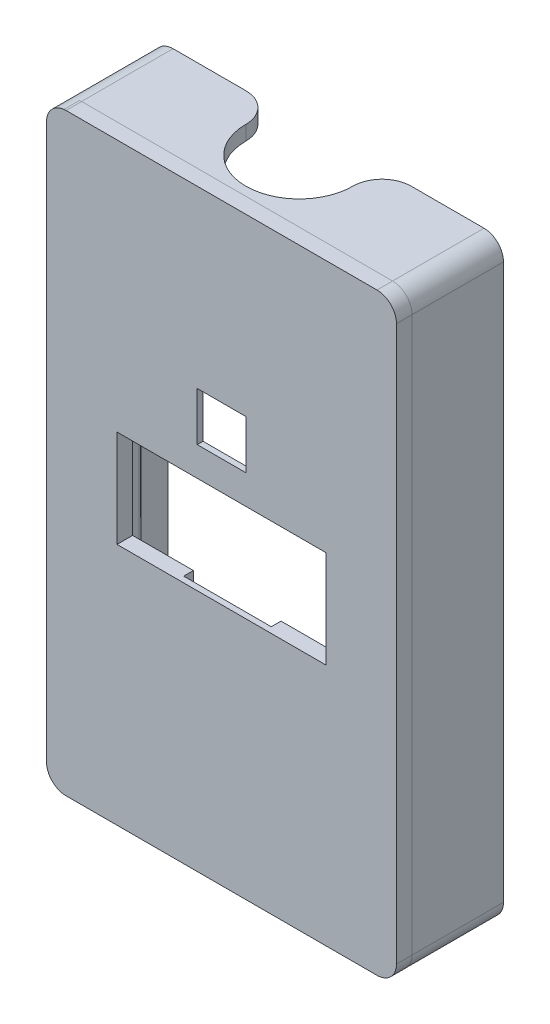
SolidWorks part; units mm, degrees
ref_plane "Спереди" through (0, 0, 0) normal (0, 0, 1) x (1, 0, 0)
ref_plane "Сверху" through (0, 0, 0) normal (0, 1, 0) x (1, 0, 0)
ref_plane "Справа" through (0, 0, 0) normal (1, 0, 0) x (0, 0, -1)
sketch "Эскиз1" plane through (0, 0, 0) normal (0, 0, 1) x (1, 0, 0)
  line L0 (0.0206, 30.5) -> (0, -30.5) construction
  line L1 (-15.9794, 30.4943) -> (15.9794, 30.4943)
  line L2 (-17.9794, 28.4943) -> (-17.9794, -28.5)
  line L3 (-15.9794, -30.5) -> (15.9794, -30.5)
  line L4 (17.9794, 28.4943) -> (17.9794, -28.5)
  line L5 (0.0103, 0) -> (-17.9794, -0.0029) construction
  line L6 (-14.028, -29) -> (14.1228, -29)
  line L7 (-14.0444, 29) -> (14.1091, 29)
  line L8 (16.5206, 26.5765) -> (16.5206, -26.5724)
  line L9 (-15.1707, 26.6651) -> (15.2053, -26.6898) construction
  line L10 (-15.1716, -26.6666) -> (15.2041, 26.6877) construction
  line L11 (-16.5, 26.5632) -> (-16.5, -26.5718)
  line L12 (-9.9794, 29) -> (-9.9027, -6.5295) construction
  line L13 (10.0196, 28.9933) -> (9.9189, -6.5362) construction
  line L14 (-9.9027, -6.5295) -> (9.9189, -6.5362) construction
  arc A0 (-17.9794, -28.5) -> (-15.9794, -30.5) centre (-15.9794, -28.5) ccw
  arc A1 (15.9794, -30.5) -> (17.9794, -28.5) centre (15.9794, -28.5) ccw
  arc A2 (17.9794, 28.4943) -> (15.9794, 30.4943) centre (15.9794, 28.4943) ccw
  circle A3 centre (-15.9794, 28.5) radius 0.7
  circle A4 centre (16.0193, 28.4892) radius 0.7
  circle A5 centre (16.0283, -28.4841) radius 0.7
  circle A6 centre (-15.9704, -28.5051) radius 0.7
  arc A7 (-15.9794, 30.4943) -> (-17.9794, 28.4943) centre (-15.9794, 28.4943) ccw
  arc A8 (14.1091, 29) -> (16.5206, 26.5765) centre (16.0193, 28.4892) ccw
  arc A9 (16.5206, -26.5724) -> (14.1228, -29) centre (16.0283, -28.4841) ccw
  arc A10 (-14.028, -29) -> (-16.5, -26.5718) centre (-15.9704, -28.5051) ccw
  arc A11 (-16.5, 26.5632) -> (-14.0444, 29) centre (-15.9794, 28.4943) ccw
  point P40 (0, 0)
  dimension "D1" = 2
extrude "Бобышка-Вытянуть1" add sketch "Эскиз1" along normal blind 11
sketch "Эскиз3" plane through (0, 0, 11) normal (0, 0, 1) x (1, 0, 0)
  line L2 (-17.9739, 28.4949) -> (-17.9739, -28.4994)
  line L3 (-15.9739, -30.4994) -> (15.985, -30.4994)
  line L4 (17.985, 28.4949) -> (17.985, -28.4994)
  line L5 (0.0158, 0.0006) -> (-17.9739, -0.0023) construction
  line L10 (-15.9739, 30.4949) -> (15.985, 30.4949)
  line L18 (-10.7342, -5.5051) -> (10.7658, -5.5051)
  line L19 (-10.7342, -5.5051) -> (-10.7342, 4.4949)
  line L20 (-10.7342, 4.4949) -> (10.7658, 4.4949)
  line L21 (10.7658, -5.5051) -> (10.7658, 4.4949)
  arc A0 (-17.9739, -28.4994) -> (-15.9739, -30.4994) centre (-15.9739, -28.4994) ccw
  arc A1 (15.985, -30.4994) -> (17.985, -28.4994) centre (15.985, -28.4994) ccw
  arc A2 (17.985, 28.4949) -> (15.985, 30.4949) centre (15.985, 28.4949) ccw
  arc A7 (-15.9739, 30.4949) -> (-17.9739, 28.4949) centre (-15.9739, 28.4949) ccw
  dimension "D1" = 2
  dimension "D2" = 21.5
  dimension "D3" = 10
  dimension "D4" = 26
extrude "Бобышка-Вытянуть2" add sketch "Эскиз3" against normal blind 1.6
sketch "Эскиз4" plane through (0, 0, 11) normal (0, 0, 1) x (1, 0, 0)
  line L0 (0.0055, 30.4949) -> (0, -30.5) construction
  line L1 (15.985, 30.4949) -> (-15.9739, 30.4949) construction
  line L2 (-15.9794, -30.5) -> (15.9794, -30.5) construction
  line L4 (-2.4963, 7.4949) -> (2.5037, 7.4949)
  line L5 (-2.4963, 7.4949) -> (-2.4963, 12.4949)
  line L6 (-2.4963, 12.4949) -> (2.5037, 12.4949)
  line L7 (2.5037, 7.4949) -> (2.5037, 12.4949)
  line L8 (-2.4963, 7.4949) -> (2.5037, 12.4949) construction
  line L9 (-2.4963, 12.4949) -> (2.5037, 7.4949) construction
  point P6 (0.0037, 9.9949)
  dimension "D1" = 5
  dimension "D2" = 5
  dimension "D3" = 20.5
extrude "Вырез-Вытянуть1" cut sketch "Эскиз4" against normal blind 1
sketch "Эскиз5" plane through (0, -30.5, 0) normal (0, -1, 0) x (1, 0, 0)
  line L0 (-15.9794, 11) -> (15.9794, 11) construction
  line L1 (3.9794, 1) -> (11.9794, 1)
  line L2 (3.9794, 1) -> (3.9794, 4)
  line L3 (3.9794, 4) -> (11.9794, 4)
  line L4 (11.9794, 1) -> (11.9794, 4)
  line L5 (3.9794, 1) -> (11.9794, 4) construction
  line L6 (3.9794, 4) -> (11.9794, 1) construction
  line L7 (17.9794, 9.4) -> (17.9794, 0) construction
  line L8 (-17.9794, 11) -> (-17.9794, 0) construction
  circle A0 centre (-10.9794, 2.5) radius 1.5
  point P0 (7.9794, 2.5)
  dimension "D5" = 7
  dimension "D1" = 8
  dimension "D2" = 3
  dimension "D3" = 7
  dimension "D4" = 6
extrude "Вырез-Вытянуть2" cut sketch "Эскиз5" against normal up to next
sketch "Эскиз6" plane through (0, 0, 9.4) normal (0, 0, -1) x (-1, 0, 0)
  line L0 (-10.7658, 4.4949) -> (10.7342, 4.4949) construction
  line L1 (-4.5182, 26.4949) -> (4.4866, 26.4949)
  line L2 (-4.5182, 26.4949) -> (-4.5182, 4.4949)
  line L3 (-4.5182, 4.4949) -> (4.4866, 4.4949)
  line L4 (4.4866, 26.4949) -> (4.4866, 4.4949)
  line L5 (-4.5182, 26.4949) -> (4.4866, 4.4949) construction
  line L6 (-4.5182, 4.4949) -> (4.4866, 26.4949) construction
  line L7 (10.7342, -5.5051) -> (-10.7658, -5.5051) construction
  line L8 (-4.5182, -5.5051) -> (4.4866, -5.5051)
  line L9 (-4.5182, -5.5051) -> (-4.5182, -26.5574)
  line L10 (-4.5182, -26.5574) -> (4.4866, -26.5574)
  line L11 (4.4866, -5.5051) -> (4.4866, -26.5574)
  point P0 (-0.0158, 15.4949)
  dimension "D1" = 22
extrude "Вырез-Вытянуть3" cut sketch "Эскиз6" against normal blind 1
sketch "Эскиз7" plane through (0, 0, 9.4) normal (0, 0, -1) x (-1, 0, 0)
  line L0 (-16.5206, -26.5724) -> (-16.5206, 26.5765) construction
  line L1 (-16.5206, 10) -> (-11.0206, 10)
  line L2 (-16.5206, 10) -> (-16.5206, -10)
  line L3 (-16.5206, -10) -> (-11.0206, -10)
  line L4 (-11.0206, 10) -> (-11.0206, -10)
  line L5 (-14.1091, 29) -> (14.0444, 29) construction
  line L6 (14.028, -29) -> (-14.1228, -29) construction
  line L7 (16.5, 26.5632) -> (16.5, -26.5718) construction
  line L8 (16.5, 10) -> (11.6, 10)
  line L9 (16.5, 10) -> (16.5, -10)
  line L10 (16.5, -10) -> (11.6, -10)
  line L11 (11.6, 10) -> (11.6, -10)
  line L12 (-16.5206, -26.5724) -> (-16.5206, 26.5765) construction
  line L13 (-6.5206, 17) -> (-4.5206, 17)
  line L14 (-6.5206, 17) -> (-6.5206, 15)
  line L15 (-6.5206, 15) -> (-4.5206, 15)
  line L16 (-4.5206, 17) -> (-4.5206, 15)
  line L17 (-0.0323, 29) -> (0, 0) construction
  line L18 (-14.1091, 29) -> (14.0444, 29) construction
  line L19 (6.4827, 17.0145) -> (6.4871, 15.0145)
  line L20 (6.4827, 17.0145) -> (4.4827, 17.01)
  line L21 (4.4827, 17.01) -> (4.4871, 15.01)
  line L22 (6.4871, 15.0145) -> (4.4871, 15.01)
  dimension "D1" = 5.5
  dimension "D2" = 20
  dimension "D3" = 19
  dimension "D4" = 19
  dimension "D5" = 4.9
  dimension "D6" = 2
  dimension "D7" = 2
  dimension "D8" = 10
  dimension "D9" = 14
extrude "Бобышка-Вытянуть4" add sketch "Эскиз7" along normal blind 2
fillet "Скругление2" radius 0.5 19 edges at (5.5206, 17, 7.4) (5.5206, 17, 9.4) (6.5206, 16, 9.4) (-5.4871, 15.0123, 7.4) (-6.4849, 16.0145, 9.4) (-5.4846, 17.0123, 9.4) (-14.05, 10, 9.4) (-16.5, 10, 8.4) (-11.6, 0, 7.4) (-16.5, 0, 7.4) (-16.5, -10, 8.4) (-14.05, -10, 9.4) (13.7706, -10, 9.4) (16.5206, -10, 8.4) (11.0206, 0, 7.4) (16.5206, 10, 8.4) (16.5206, 0, 7.4) (13.7706, 10, 9.4) (5.5206, 15, 7.4)
sketch "Эскиз9" plane through (0, 30.4943, 0) normal (0, 1, 0) x (1, 0, 0)
  line L0 (0, 0) -> (0, -3) construction
  circle A0 centre (0, -3) radius 5.5
  dimension "D1" = 3
extrude "Вырез-Вытянуть4" cut sketch "Эскиз9" against normal up to next
fillet "Скругление3" radius 3 2 edges at (4.6098, 29.7471, 0) (-4.6098, 29.7471, 0)
